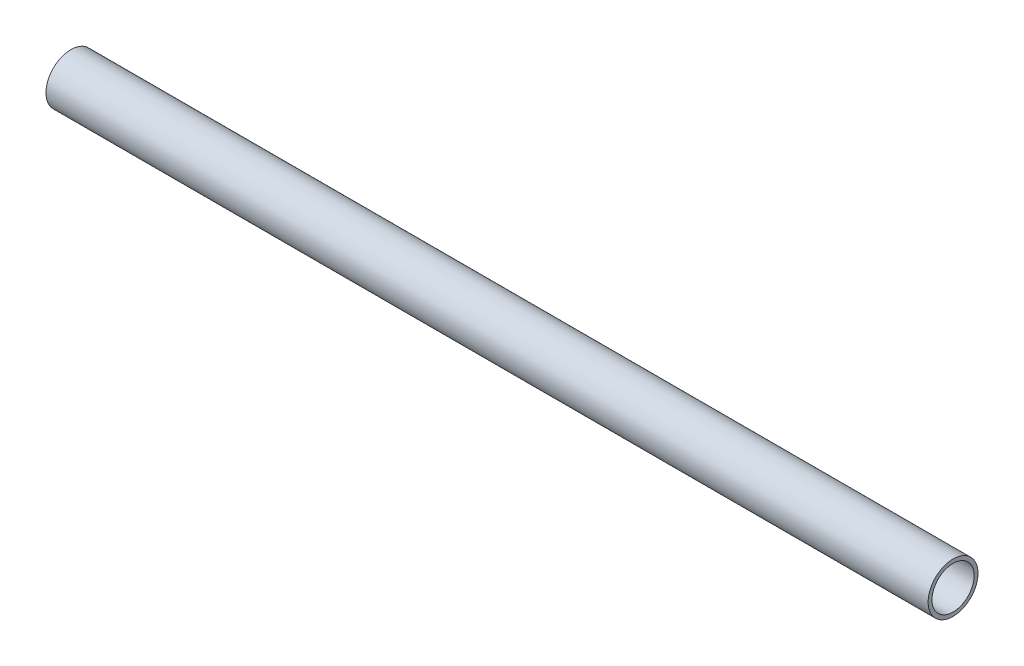
SolidWorks part; units mm, degrees
material "1060 合金"
ref_plane "前视基准面" through (0, 0, 0) normal (0, 0, 1) x (1, 0, 0)
ref_plane "上视基准面" through (0, 0, 0) normal (0, 1, 0) x (1, 0, 0)
ref_plane "右视基准面" through (0, 0, 0) normal (1, 0, 0) x (0, 0, -1)
sketch "草图1" plane through (0, 0, 0) normal (1, 0, 0) x (0, 0, -1)
  circle A0 centre (0, 0) radius 13
  circle A1 centre (0, 0) radius 11
  dimension "D1" = 22
  dimension "D2" = 26
extrude "凸台-拉伸1" add sketch "草图1" along normal blind 460
sketch "草图2" plane through (0, 0, 0) normal (0, 0, 1) x (1, 0, 0)
  line L0 (0, 0) -> (64.4782, 0) construction
  line L1 (0, 13) -> (0, -13) construction
  line L2 (460, -13) -> (460, 13) construction
  circle A0 centre (21, 0) radius 2
  circle A1 centre (445, 0) radius 2.5
  dimension "D1" = 4
  dimension "D3" = 15
  dimension "D2" = 21
extrude "切除-拉伸1" cut sketch "草图2" against normal through all
sketch "草图4" plane through (0, 0, 0) normal (0, 1, 0) x (1, 0, 0)
  line L0 (0, 0) -> (460, 0) construction
  line L1 (460, -13) -> (460, 13) construction
  line L2 (0, 13) -> (0, -13) construction
  circle A0 centre (12.5, 0) radius 1.5
  circle A1 centre (441.5, 0) radius 1.5
  dimension "D2" = 3
  dimension "D3" = 3
  dimension "D1" = 12.5
  dimension "D4" = 18.5
extrude "切除-拉伸2" cut sketch "草图4" against normal through all
